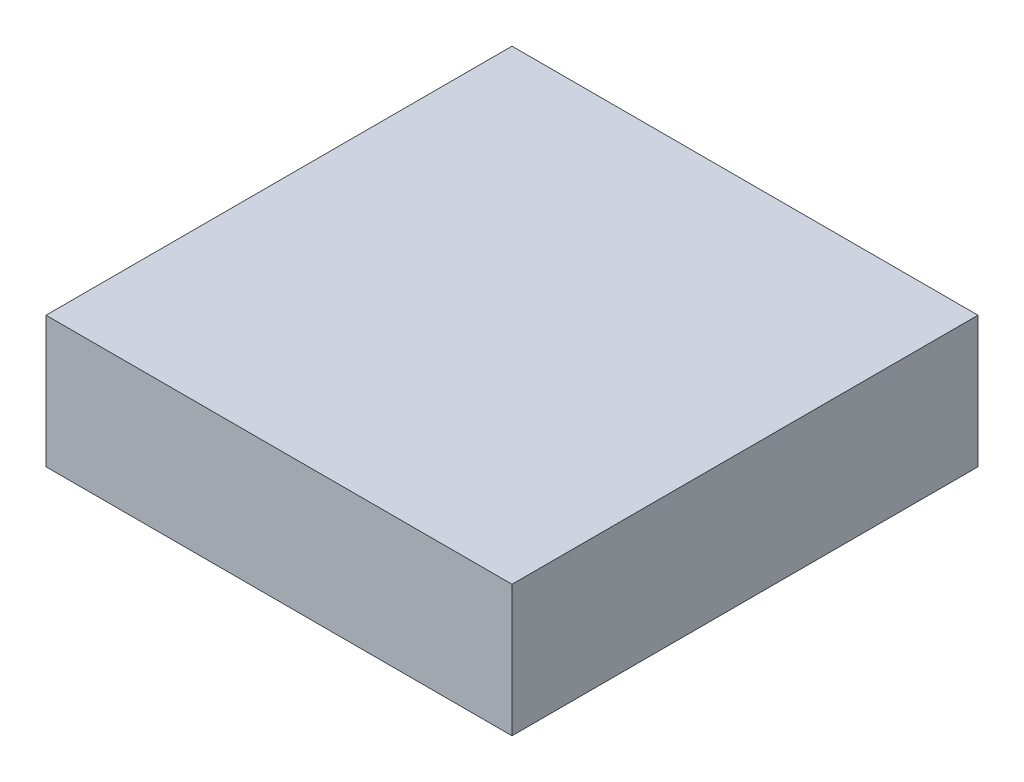
SolidWorks part; units mm, degrees
ref_plane "Ebene vorne" through (0, 0, 0) normal (0, 0, 1) x (1, 0, 0)
ref_plane "Ebene oben" through (0, 0, 0) normal (0, 1, 0) x (1, 0, 0)
ref_plane "Ebene rechts" through (0, 0, 0) normal (1, 0, 0) x (0, 0, -1)
sketch "Skizze1" plane through (0, 0, 0) normal (0, 1, 0) x (1, 0, 0)
  line L1 (-8.875, 8.875) -> (8.875, 8.875)
  line L2 (-8.875, 8.875) -> (-8.875, -8.875)
  line L3 (-8.875, -8.875) -> (8.875, -8.875)
  line L4 (8.875, 8.875) -> (8.875, -8.875)
  point P4 (0, 8.875)
  point P6 (8.875, 0)
  dimension "D1" = 17.75
  dimension "D2" = 17.75
extrude "Aufsatz-Linear austragen1" add sketch "Skizze1" along normal blind 5
